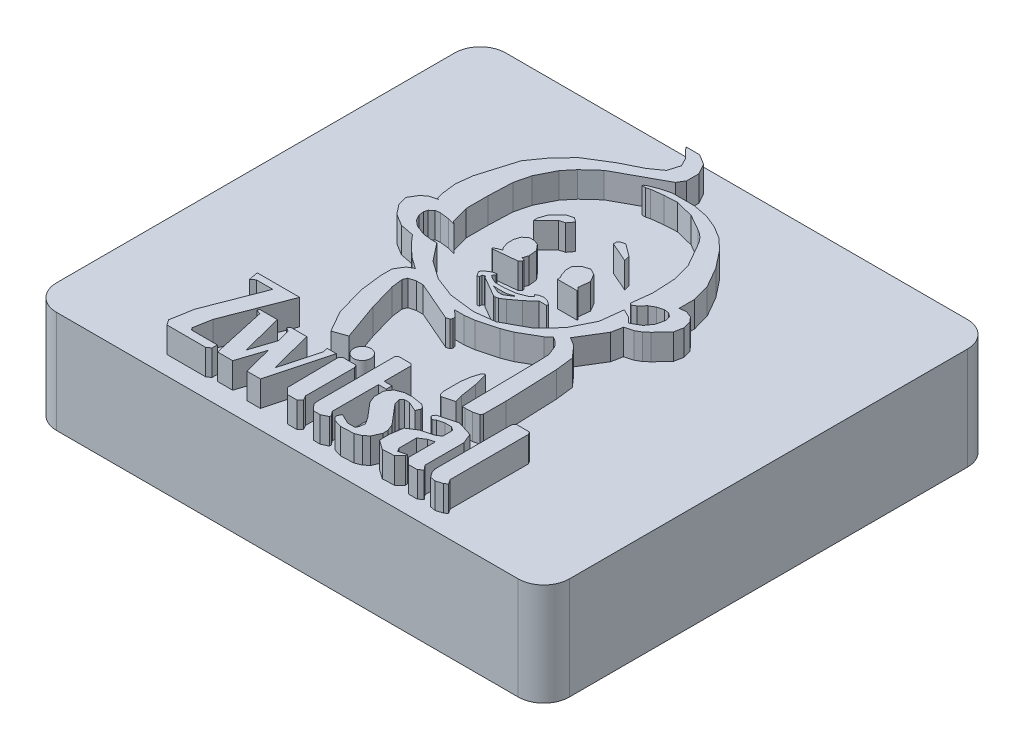
SolidWorks part; units mm, degrees
ref_plane "Front Plane" through (0, 0, 0) normal (0, 0, 1) x (1, 0, 0)
ref_plane "Top Plane" through (0, 0, 0) normal (0, 1, 0) x (1, 0, 0)
ref_plane "Right Plane" through (0, 0, 0) normal (1, 0, 0) x (0, 0, -1)
sketch "Sketch1" plane through (0, 0, 0) normal (0, 1, 0) x (1, 0, 0)
  line L1 (-100.2137, -87.7872) -> (100.2137, -87.7872)
  line L2 (-100.2137, -87.7872) -> (-100.2137, 87.7872)
  line L3 (-100.2137, 87.7872) -> (100.2137, 87.7872)
  line L4 (100.2137, -87.7872) -> (100.2137, 87.7872)
  line L5 (-100.2137, -87.7872) -> (100.2137, 87.7872) construction
  line L6 (-100.2137, 87.7872) -> (100.2137, -87.7872) construction
  point P0 (0, 0)
extrude "Boss-Extrude1" add sketch "Sketch1" along normal blind 40
fillet "Fillet1" radius 10 1 edges at (-100.2137, 20, -87.7872)
fillet "Fillet2" radius 10 1 edges at (100.2137, 20, -87.7872)
fillet "Fillet3" radius 10 1 edges at (100.2137, 20, 87.7872)
fillet "Fillet4" radius 10 1 edges at (-100.2137, 20, 87.7872)
sketch "Sketch2" plane through (0, 40, 0) normal (0, 1, 0) x (1, 0, 0)
  line L0 (306.3054, 1187.5992) -> (1789.6387, 1187.5992) construction
  line L1 (-54.3505, -45.1953) -> (-37.775, -45.1953)
  line L2 (-37.775, -45.1953) -> (-47.2756, -69.6543)
  line L3 (-47.2756, -69.6543) -> (-48.4884, -76.5271)
  line L4 (-48.4884, -76.5271) -> (-47.882, -77.3934)
  line L5 (-47.882, -77.3934) -> (-40.706, -77.3934)
  line L6 (-40.706, -77.3934) -> (-37.775, -77.3934)
  line L7 (-37.775, -77.3934) -> (-37.775, -79.4581)
  line L8 (-37.775, -79.4581) -> (-39.2405, -80.484)
  line L9 (-39.2405, -80.484) -> (-54.3505, -80.484)
  line L10 (-54.3505, -80.484) -> (-55.7913, -78.4258)
  line L11 (-55.7913, -78.4258) -> (-54.2433, -69.6543)
  line L12 (-54.2433, -69.6543) -> (-45.7365, -47.7536)
  line L13 (-45.7365, -47.7536) -> (-52.127, -47.7536)
  line L14 (-52.127, -47.7536) -> (-53.6655, -48.8306)
  line L15 (-53.6655, -48.8306) -> (-54.3505, -45.1953)
  line L16 (-41.5367, -57.1064) -> (-34.5884, -57.1064)
  line L17 (-34.5884, -57.1064) -> (-30.3919, -73.5484)
  line L18 (-30.3919, -73.5484) -> (-27.2443, -63.9885)
  line L19 (-27.2443, -63.9885) -> (-28.5356, -58.929)
  line L20 (-28.5356, -58.929) -> (-29.9995, -58.0604)
  line L21 (-29.9995, -58.0604) -> (-29.4334, -57.1064)
  line L22 (-29.4334, -57.1064) -> (-23.0997, -57.1064)
  line L23 (-23.0997, -57.1064) -> (-18.7793, -74.0335)
  line L24 (-18.7793, -74.0335) -> (-14.7067, -58.929)
  line L25 (-14.7067, -58.929) -> (-15.0501, -57.5834)
  line L26 (-15.0501, -57.5834) -> (-15.0501, -57.1064)
  line L27 (-15.0501, -57.1064) -> (-11.5421, -57.1064)
  line L28 (-11.5421, -57.1064) -> (-17.8455, -80.484)
  line L29 (-17.8455, -80.484) -> (-23.0997, -80.484)
  line L30 (-23.0997, -80.484) -> (-25.9729, -69.2263)
  line L31 (-25.9729, -69.2263) -> (-29.4334, -79.7361)
  line L32 (-29.4334, -79.7361) -> (-35.3452, -79.7361)
  line L33 (-35.3452, -79.7361) -> (-40.028, -58.4947)
  line L34 (-40.028, -58.4947) -> (-41.8031, -57.9103)
  line L35 (-41.8031, -57.9103) -> (-41.5367, -57.1064)
  line L36 (-9.0614, -57.1064) -> (-3.85, -57.1064)
  line L37 (-3.85, -57.1064) -> (-3.2808, -58.1815)
  line L38 (-3.2808, -58.1815) -> (-3.2808, -77.3934)
  line L39 (-3.2808, -77.3934) -> (-2.2898, -79.2654)
  line L40 (-2.2898, -79.2654) -> (-3.5654, -80.484)
  line L41 (-3.5654, -80.484) -> (-7.3461, -80.484)
  line L42 (-7.3461, -80.484) -> (-9.6446, -78.0779)
  line L43 (-9.6446, -78.0779) -> (-9.8746, -58.1815)
  line L44 (-9.8746, -58.1815) -> (-9.0614, -57.1064)
  line L45 (1.5966, -45.8731) -> (6.4741, -45.8731)
  line L46 (6.4741, -45.8731) -> (7.1619, -46.5609)
  line L47 (7.1619, -46.5609) -> (7.1619, -57.1064)
  line L48 (7.1619, -57.1064) -> (10.226, -57.1064)
  line L49 (10.226, -57.1064) -> (10.226, -59.3383)
  line L50 (10.226, -59.3383) -> (7.1619, -59.3383)
  line L51 (7.1619, -59.3383) -> (7.1619, -77.3934)
  line L52 (7.1619, -77.3934) -> (8.4015, -79.013)
  line L53 (8.4015, -79.013) -> (8.4015, -79.7361)
  line L54 (8.4015, -79.7361) -> (5.95, -80.8893)
  line L55 (5.95, -80.8893) -> (3.2634, -80.8893)
  line L56 (3.2634, -80.8893) -> (1.0295, -78.4258)
  line L57 (1.0295, -78.4258) -> (0.8619, -76.2764)
  line L58 (0.8619, -76.2764) -> (0.8619, -46.5609)
  line L59 (0.8619, -46.5609) -> (1.5966, -45.8731)
  line L60 (23.7545, -59.3383) -> (23.0196, -60.9979)
  line L61 (23.0196, -60.9979) -> (20.527, -59.8941)
  line L62 (20.527, -59.8941) -> (19.2719, -59.3383)
  line L63 (19.2719, -59.3383) -> (17.3668, -59.3383)
  line L64 (17.3668, -59.3383) -> (16.2592, -60.446)
  line L65 (16.2592, -60.446) -> (16.813, -62.5241)
  line L66 (16.813, -62.5241) -> (23.3871, -70.2685)
  line L67 (23.3871, -70.2685) -> (24.4894, -72.9818)
  line L68 (24.4894, -72.9818) -> (24.4894, -74.9038)
  line L69 (24.4894, -74.9038) -> (23.611, -76.8874)
  line L70 (23.611, -76.8874) -> (23.0196, -78.2229)
  line L71 (23.0196, -78.2229) -> (21.237, -79.7361)
  line L72 (21.237, -79.7361) -> (18.9465, -80.6667)
  line L73 (18.9465, -80.6667) -> (13.7794, -80.8893)
  line L74 (13.7794, -80.8893) -> (10.8865, -79.97)
  line L75 (10.8865, -79.97) -> (9.6031, -78.6866)
  line L76 (9.6031, -78.6866) -> (9.6031, -77.8905)
  line L77 (9.6031, -77.8905) -> (10.2448, -76.5271)
  line L78 (10.2448, -76.5271) -> (11.6931, -77.2088)
  line L79 (11.6931, -77.2088) -> (14.1715, -78.3753)
  line L80 (14.1715, -78.3753) -> (17.0524, -78.3753)
  line L81 (17.0524, -78.3753) -> (17.6014, -77.2088)
  line L82 (17.6014, -77.2088) -> (17.9127, -75.1628)
  line L83 (17.9127, -75.1628) -> (16.3629, -72.7591)
  line L84 (16.3629, -72.7591) -> (11.5018, -67.0327)
  line L85 (11.5018, -67.0327) -> (10.368, -64.2417)
  line L86 (10.368, -64.2417) -> (10.368, -60.446)
  line L87 (10.368, -60.446) -> (11.9809, -58.1815)
  line L88 (11.9809, -58.1815) -> (14.9883, -56.9598)
  line L89 (14.9883, -56.9598) -> (17.9127, -56.8337)
  line L90 (17.9127, -56.8337) -> (22.1283, -57.4752)
  line L91 (22.1283, -57.4752) -> (23.3871, -58.3718)
  line L92 (23.3871, -58.3718) -> (23.7545, -59.3383)
  line L93 (28.8189, -58.3718) -> (35.9344, -56.4755)
  line L94 (35.9344, -56.4755) -> (41.9018, -58.3718)
  line L95 (41.9018, -58.3718) -> (43.5155, -62.3438)
  line L96 (43.5155, -62.3438) -> (43.5155, -77.5551)
  line L97 (43.5155, -77.5551) -> (44.9812, -79.2817)
  line L98 (44.9812, -79.2817) -> (43.5155, -80.5259)
  line L99 (43.5155, -80.5259) -> (40.0158, -80.5259)
  line L100 (40.0158, -80.5259) -> (37.6572, -78.1672)
  line L101 (37.6572, -78.1672) -> (37.6572, -72.9818)
  line L102 (37.6572, -72.9818) -> (37.6572, -67.6324)
  line L103 (37.6572, -67.6324) -> (35.267, -68.2694)
  line L104 (35.267, -68.2694) -> (32.6613, -69.9495)
  line L105 (32.6613, -69.9495) -> (32.6613, -76.8874)
  line L106 (32.6613, -76.8874) -> (33.4866, -78.1672)
  line L107 (33.4866, -78.1672) -> (35.267, -77.6927)
  line L108 (35.267, -77.6927) -> (36.4621, -77.3742)
  line L109 (36.4621, -77.3742) -> (36.4621, -78.1672)
  line L110 (36.4621, -78.1672) -> (34.3768, -80.2525)
  line L111 (34.3768, -80.2525) -> (29.8284, -80.5259)
  line L112 (29.8284, -80.5259) -> (26.1285, -77.8905)
  line L113 (26.1285, -77.8905) -> (26.1285, -73.9428)
  line L114 (26.1285, -73.9428) -> (26.8639, -69.1094)
  line L115 (26.8639, -69.1094) -> (30.5763, -66.7158)
  line L116 (30.5763, -66.7158) -> (35.267, -65.4657)
  line L117 (35.267, -65.4657) -> (37.1653, -64.2417)
  line L118 (37.1653, -64.2417) -> (37.1653, -60.3578)
  line L119 (37.1653, -60.3578) -> (35.734, -59.3383)
  line L120 (35.734, -59.3383) -> (33.074, -59.3383)
  line L121 (33.074, -59.3383) -> (30.5763, -60.0039)
  line L122 (30.5763, -60.0039) -> (29.4478, -60.7316)
  line L123 (29.4478, -60.7316) -> (27.9785, -59.685)
  line L124 (27.9785, -59.685) -> (28.8189, -58.3718)
  line L125 (47.6216, -45.8731) -> (52.7453, -45.8731)
  line L126 (52.7453, -45.8731) -> (53.3033, -46.9209)
  line L127 (53.3033, -46.9209) -> (53.3033, -77.5551)
  line L128 (53.3033, -77.5551) -> (54.5152, -79.2817)
  line L129 (54.5152, -79.2817) -> (53.3033, -80.1323)
  line L130 (53.3033, -80.1323) -> (50.8305, -80.8893)
  line L131 (50.8305, -80.8893) -> (48.7016, -80.5108)
  line L132 (48.7016, -80.5108) -> (47.233, -78.4184)
  line L133 (47.233, -78.4184) -> (46.7643, -76.8874)
  line L134 (46.7643, -76.8874) -> (46.7643, -46.9209)
  line L135 (46.7643, -46.9209) -> (47.6216, -45.8731)
  line L136 (-13.1432, 81.2221) -> (-7.9144, 81.2221)
  line L137 (-7.9144, 81.2221) -> (-3.8492, 78.7248)
  line L138 (-3.8492, 78.7248) -> (-1.5929, 74.5885)
  line L139 (-1.5929, 74.5885) -> (-1.5929, 69.8279)
  line L140 (-1.5929, 69.8279) -> (-3.28, 67.0817)
  line L141 (-3.28, 67.0817) -> (-8.442, 64.2658)
  line L142 (-8.442, 64.2658) -> (-21.2696, 57.2684)
  line L143 (-21.2696, 57.2684) -> (-26.6675, 52.3283)
  line L144 (-26.6675, 52.3283) -> (-29.9986, 48.3481)
  line L145 (-29.9986, 48.3481) -> (-33.4907, 41.3937)
  line L146 (-33.4907, 41.3937) -> (-34.9864, 35.4394)
  line L147 (-34.9864, 35.4394) -> (-35.3444, 25.9167)
  line L148 (-35.3444, 25.9167) -> (-35.3444, 17.4167)
  line L149 (-35.3444, 17.4167) -> (-33.4907, 10.6168)
  line L150 (-33.4907, 10.6168) -> (-32.4808, 9.7716)
  line L151 (-32.4808, 9.7716) -> (-35.3444, 10.491)
  line L152 (-35.3444, 10.491) -> (-38.9083, 10.9209)
  line L153 (-38.9083, 10.9209) -> (-40.7052, 10.7059)
  line L154 (-40.7052, 10.7059) -> (-42.165, 9.3699)
  line L155 (-42.165, 9.3699) -> (-42.5251, 7.9364)
  line L156 (-42.5251, 7.9364) -> (-42.2834, 5.9158)
  line L157 (-42.2834, 5.9158) -> (-41.1194, 3.7819)
  line L158 (-41.1194, 3.7819) -> (-38.9083, 1.9314)
  line L159 (-38.9083, 1.9314) -> (-34.9864, 0.4291)
  line L160 (-34.9864, 0.4291) -> (-31.7446, 0.0381)
  line L161 (-31.7446, 0.0381) -> (-29.4326, 0.0381)
  line L162 (-29.4326, 0.0381) -> (-23.9686, -6.8987)
  line L163 (-23.9686, -6.8987) -> (-17.0316, -11.8156)
  line L164 (-17.0316, -11.8156) -> (-9.0606, -14.8688)
  line L165 (-9.0606, -14.8688) -> (-5.0221, -15.356)
  line L166 (-5.0221, -15.356) -> (0.8627, -16.0658)
  line L167 (0.8627, -16.0658) -> (8.8331, -15.1124)
  line L168 (8.8331, -15.1124) -> (18.4848, -9.8474)
  line L169 (18.4848, -9.8474) -> (24.4902, -3.4303)
  line L170 (24.4902, -3.4303) -> (28.8197, 5.1921)
  line L171 (28.8197, 5.1921) -> (29.6782, 12.3093)
  line L172 (29.6782, 12.3093) -> (29.8842, 14.0168)
  line L173 (29.8842, 14.0168) -> (31.1085, 13.402)
  line L174 (31.1085, 13.402) -> (33.0748, 12.4147)
  line L175 (33.0748, 12.4147) -> (34.671, 10.9209)
  line L176 (34.671, 10.9209) -> (35.2678, 10.3623)
  line L177 (35.2678, 10.3623) -> (38.8538, 12.4147)
  line L178 (38.8538, 12.4147) -> (40.7565, 15.0992)
  line L179 (40.7565, 15.0992) -> (41.62, 18.5366)
  line L180 (41.62, 18.5366) -> (41.0725, 20.545)
  line L181 (41.0725, 20.545) -> (39.49, 21.6667)
  line L182 (39.49, 21.6667) -> (37.658, 21.8877)
  line L183 (37.658, 21.8877) -> (35.2678, 21.2361)
  line L184 (35.2678, 21.2361) -> (33.0748, 19.9809)
  line L185 (33.0748, 19.9809) -> (31.0196, 17.7849)
  line L186 (31.0196, 17.7849) -> (29.5478, 16.9425)
  line L187 (29.5478, 16.9425) -> (28.8197, 17.4586)
  line L188 (28.8197, 17.4586) -> (29.755, 25.2122)
  line L189 (29.755, 25.2122) -> (29.2874, 34.5514)
  line L190 (29.2874, 34.5514) -> (27.4221, 41.3937)
  line L191 (27.4221, 41.3937) -> (22.1291, 50.6417)
  line L192 (17.3676, 55.3916) -> (11.0575, 58.9828)
  line L193 (11.0575, 58.9828) -> (3.9528, 60.7676)
  line L194 (3.9528, 60.7676) -> (-1.031, 60.518)
  line L195 (-1.031, 60.518) -> (-5.8619, 59.9401)
  line L196 (-5.8619, 59.9401) -> (-7.3461, 59.5355)
  line L197 (-7.3461, 59.5355) -> (-8.6735, 59.5355)
  line L198 (-8.6735, 59.5355) -> (-8.5719, 59.9401)
  line L199 (-8.5719, 59.9401) -> (-7.3461, 60.6417)
  line L200 (-7.3461, 60.6417) -> (-4.4076, 61.7795)
  line L201 (-4.4076, 61.7795) -> (-0.2695, 62.9076)
  line L202 (-0.2695, 62.9076) -> (3.8457, 62.9076)
  line L203 (3.8457, 62.9076) -> (8.4015, 62.9076)
  line L204 (8.4015, 62.9076) -> (14.2122, 61.7795)
  line L205 (14.2122, 61.7795) -> (19.2719, 59.7378)
  line L206 (19.2719, 59.7378) -> (24.047, 56.8043)
  line L207 (24.047, 56.8043) -> (28.232, 52.8878)
  line L208 (28.232, 52.8878) -> (33.6807, 45.9705)
  line L209 (33.6807, 45.9705) -> (38.258, 37.973)
  line L210 (38.258, 37.973) -> (40.0832, 31.2775)
  line L211 (40.0832, 31.2775) -> (40.0832, 25.2126)
  line L212 (40.0832, 25.2126) -> (42.7254, 25.5287)
  line L213 (42.7254, 25.5287) -> (45.2017, 24.5295)
  line L214 (45.2017, 24.5295) -> (46.7643, 22.7357)
  line L215 (46.7643, 22.7357) -> (47.6216, 19.5908)
  line L216 (47.6216, 19.5908) -> (46.9531, 16.1475)
  line L217 (46.9531, 16.1475) -> (44.7159, 13.7569)
  line L218 (44.7159, 13.7569) -> (42.7254, 11.63)
  line L219 (42.7254, 11.63) -> (40.8901, 10.0312)
  line L220 (40.8901, 10.0312) -> (38.8538, 8.8658)
  line L221 (38.8538, 8.8658) -> (35.6149, 7.9828)
  line L222 (35.6149, 7.9828) -> (34.7993, 3.7819)
  line L223 (34.7993, 3.7819) -> (32.476, 0)
  line L224 (32.476, 0) -> (29.9483, -4.1144)
  line L225 (29.9483, -4.1144) -> (28.8197, -5.9515)
  line L226 (28.8197, -5.9515) -> (32.0916, -7.9615)
  line L227 (32.0916, -7.9615) -> (36.0275, -12.4799)
  line L228 (36.0275, -12.4799) -> (36.8599, -19.4386)
  line L229 (36.8599, -19.4386) -> (37.6572, -39.9253)
  line L230 (37.6572, -39.9253) -> (37.6572, -48.8306)
  line L231 (37.6572, -48.8306) -> (37.1653, -49.6311)
  line L232 (37.1653, -49.6311) -> (34.7993, -50.2761)
  line L233 (34.7993, -50.2761) -> (32.0916, -50.3815)
  line L234 (32.0916, -50.3815) -> (30.9564, -50.3815)
  line L235 (30.9564, -50.3815) -> (30.9042, -49.0402)
  line L236 (30.9042, -49.0402) -> (30.4557, -20.2047)
  line L237 (30.4557, -20.2047) -> (30.2905, -15.9593)
  line L238 (30.2905, -15.9593) -> (28.8197, -12.1611)
  line L239 (28.8197, -12.1611) -> (27.1295, -10.2207)
  line L240 (27.1295, -10.2207) -> (25.3141, -9.1055)
  line L241 (25.3141, -9.1055) -> (23.3871, -10.7841)
  line L242 (23.3871, -10.7841) -> (20.0406, -12.6995)
  line L243 (20.0406, -12.6995) -> (15.8247, -15.1124)
  line L244 (15.8247, -15.1124) -> (11.9809, -16.6008)
  line L245 (11.9809, -16.6008) -> (7.8652, -17.7227)
  line L246 (7.8652, -17.7227) -> (4.2854, -18.6986)
  line L247 (4.2854, -18.6986) -> (0.4904, -19.1526)
  line L248 (0.4904, -19.1526) -> (-3.2808, -19.1526)
  line L249 (-3.2808, -19.1526) -> (-2.0797, -20.2767)
  line L250 (-2.0797, -20.2767) -> (-0.8546, -21.4231)
  line L251 (-0.8546, -21.4231) -> (-0.5877, -22.4022)
  line L252 (-0.5877, -22.4022) -> (-1.0954, -23.2285)
  line L253 (-1.0954, -23.2285) -> (-2.3579, -23.5727)
  line L254 (-2.3579, -23.5727) -> (-14.7067, -18.2107)
  line L255 (-14.7067, -18.2107) -> (-17.8455, -16.8477)
  line L256 (-17.8455, -16.8477) -> (-20.5001, -16.8477)
  line L257 (-20.5001, -16.8477) -> (-23.0997, -17.5564)
  line L258 (-23.0997, -17.5564) -> (-23.7927, -19.1526)
  line L259 (-23.7927, -19.1526) -> (-23.264, -23.5727)
  line L260 (-23.264, -23.5727) -> (-20.2499, -34.0623)
  line L261 (-20.2499, -34.0623) -> (-15.0501, -48.6693)
  line L262 (-15.0501, -48.6693) -> (-20.2499, -50.5203)
  line L263 (-20.2499, -50.5203) -> (-24.9503, -42.3077)
  line L264 (-24.9503, -42.3077) -> (-28.2875, -30.694)
  line L265 (-28.2875, -30.694) -> (-29.3379, -21.9127)
  line L266 (-29.3379, -21.9127) -> (-29.3379, -17.5564)
  line L267 (-29.3379, -17.5564) -> (-27.2443, -14.1484)
  line L268 (-27.2443, -14.1484) -> (-24.9503, -12.8355)
  line L269 (-24.9503, -12.8355) -> (-29.3379, -9.7256)
  line L270 (-29.3379, -9.7256) -> (-33.9126, -5.4444)
  line L271 (-33.9126, -5.4444) -> (-36.9474, -1.9606)
  line L272 (-36.9474, -1.9606) -> (-42.2834, -0.9246)
  line L273 (-42.2834, -0.9246) -> (-46.9323, 1.9314)
  line L274 (-46.9323, 1.9314) -> (-49.8417, 5.625)
  line L275 (-49.8417, 5.625) -> (-50.8626, 9.3699)
  line L276 (-50.8626, 9.3699) -> (-48.8079, 12.7145)
  line L277 (-48.8079, 12.7145) -> (-46.9323, 14.1919)
  line L278 (-46.9323, 14.1919) -> (-43.6041, 15.0992)
  line L279 (-43.6041, 15.0992) -> (-44.3738, 15.2486)
  line L280 (-44.3738, 15.2486) -> (-45.0652, 17.7849)
  line L281 (-45.0652, 17.7849) -> (-45.7647, 23.6326)
  line L282 (-45.7647, 23.6326) -> (-45.0109, 29.8818)
  line L283 (-45.0109, 29.8818) -> (-40.7052, 44.3054)
  line L284 (-40.7052, 44.3054) -> (-36.4291, 50.3382)
  line L285 (-36.4291, 50.3382) -> (-30.5886, 56.5791)
  line L286 (-30.5886, 56.5791) -> (-21.2696, 62.3436)
  line L287 (-21.2696, 62.3436) -> (-13.7226, 66.0996)
  line L288 (-13.7226, 66.0996) -> (-9.0606, 69.4328)
  line L289 (-9.0606, 69.4328) -> (-7.7178, 73.9309)
  line L290 (-7.7178, 73.9309) -> (-9.3636, 77.2377)
  line L291 (-9.3636, 77.2377) -> (-11.8031, 79.5207)
  line L292 (-11.8031, 79.5207) -> (-13.1432, 81.2221)
  line L293 (23.3871, -51.1888) -> (27.9785, -49.9319)
  line L294 (27.9785, -49.9319) -> (27.1295, -46.8307)
  line L295 (27.1295, -46.8307) -> (26.1285, -40.409)
  line L296 (26.1285, -40.409) -> (24.9285, -36.0255)
  line L297 (24.9285, -36.0255) -> (24.6665, -35.0683)
  line L298 (24.6665, -35.0683) -> (24.221, -35.0683)
  line L299 (24.221, -35.0683) -> (23.611, -35.6783)
  line L300 (23.611, -35.6783) -> (22.6673, -38.5596)
  line L301 (22.6673, -38.5596) -> (22.1283, -42.3077)
  line L302 (22.1283, -42.3077) -> (22.1283, -46.5609)
  line L303 (22.1283, -46.5609) -> (22.1283, -49.0402)
  line L304 (22.1283, -49.0402) -> (22.5444, -50.5603)
  line L305 (22.5444, -50.5603) -> (23.3871, -51.1888)
  line L306 (-11.019, 35.4394) -> (-13.7226, 34.6994)
  line L307 (-13.7226, 34.6994) -> (-17.0316, 31.3903)
  line L308 (-17.0316, 31.3903) -> (-18.1221, 28.0609)
  line L309 (-18.1221, 28.0609) -> (-18.1221, 26.4302)
  line L310 (-18.1221, 26.4302) -> (-15.3771, 29.1753)
  line L311 (-15.3771, 29.1753) -> (-13.1432, 31.4092)
  line L312 (-13.1432, 31.4092) -> (-11.019, 31.9906)
  line L313 (-11.019, 31.9906) -> (-9.3636, 34.2104)
  line L314 (-9.3636, 34.2104) -> (-11.019, 35.4394)
  line L315 (5.4321, 34.2104) -> (13.235, 30.7868)
  line L316 (13.235, 30.7868) -> (12.6017, 33.1005)
  line L317 (12.6017, 33.1005) -> (10.226, 34.8644)
  line L318 (10.226, 34.8644) -> (7.8652, 36.6172)
  line L319 (7.8652, 36.6172) -> (5.95, 36.0929)
  line L320 (5.95, 36.0929) -> (5.4321, 35.3955)
  line L321 (5.4321, 35.3955) -> (5.4321, 34.2104)
  line L322 (-16.4181, 8.8658) -> (-7.3461, 9.7716)
  line L323 (-7.3461, 9.7716) -> (-6.5625, 10.7291)
  line L324 (-6.5625, 10.7291) -> (-6.6176, 11.281)
  line L325 (-6.6176, 11.281) -> (-7.7178, 11.63)
  line L326 (-7.7178, 11.63) -> (-7.0432, 13.7569)
  line L327 (-7.0432, 13.7569) -> (-7.3613, 16.9425)
  line L328 (-7.3613, 16.9425) -> (-9.3636, 19.2824)
  line L329 (-9.3636, 19.2824) -> (-11.2844, 19.8916)
  line L330 (-11.2844, 19.8916) -> (-13.1432, 19.8916)
  line L331 (-13.1432, 19.8916) -> (-14.861, 18.4217)
  line L332 (-14.861, 18.4217) -> (-15.5823, 16.1475)
  line L333 (-15.5823, 16.1475) -> (-15.5823, 13.7569)
  line L334 (-15.5823, 13.7569) -> (-14.861, 11.4555)
  line L335 (-14.861, 11.4555) -> (-14.0021, 10.4517)
  line L336 (-14.0021, 10.4517) -> (-15.8923, 9.8593)
  line L337 (-15.8923, 9.8593) -> (-16.8264, 9.06)
  line L338 (-16.8264, 9.06) -> (-16.4181, 8.8658)
  line L339 (6.4741, 11.281) -> (14.2122, 11.281)
  line L340 (14.2122, 11.281) -> (14.2122, 11.63)
  line L341 (14.2122, 11.63) -> (13.235, 12.6071)
  line L342 (13.235, 12.6071) -> (13.7236, 16.9425)
  line L343 (13.7236, 16.9425) -> (11.9809, 19.9809)
  line L344 (11.9809, 19.9809) -> (9.6031, 21.2361)
  line L345 (9.6031, 21.2361) -> (6.9002, 20.4009)
  line L346 (6.9002, 20.4009) -> (4.961, 18.4617)
  line L347 (4.961, 18.4617) -> (4.961, 16.1475)
  line L348 (4.961, 16.1475) -> (5.6997, 13.7569)
  line L349 (5.6997, 13.7569) -> (6.4741, 12.4068)
  line L350 (6.4741, 12.4068) -> (6.4741, 11.281)
  line L351 (-7.7178, -0.2665) -> (-7.0432, 0.7197)
  line L352 (-7.0432, 0.7197) -> (-7.1595, 1.3394)
  line L353 (-7.1595, 1.3394) -> (-8.6735, 1.0296)
  line L354 (-8.6735, 1.0296) -> (-10.2948, 0)
  line L355 (-10.2948, 0) -> (-11.2844, -0.9246)
  line L356 (-11.2844, -0.9246) -> (-11.5421, -1.5235)
  line L357 (-11.5421, -1.5235) -> (-10.5329, -3.1127)
  line L358 (-10.5329, -3.1127) -> (-9.6446, -3.1127)
  line L359 (-9.6446, -3.1127) -> (-9.6446, -2.074)
  line L360 (-9.6446, -2.074) -> (-9.0606, -1.7031)
  line L361 (-9.0606, -1.7031) -> (-8.442, -1.8412)
  line L362 (-8.442, -1.8412) -> (-8.442, -2.1477)
  line L363 (-8.442, -2.1477) -> (-0.5877, -6.6769)
  line L364 (-0.5877, -6.6769) -> (0.2786, -6.8703)
  line L365 (0.2786, -6.8703) -> (1.3726, -6.6464)
  line L366 (1.3726, -6.6464) -> (3.2634, -5.4457)
  line L367 (3.2634, -5.4457) -> (6.9002, -2.7859)
  line L368 (6.9002, -2.7859) -> (9.6031, -0.2605)
  line L369 (9.6031, -0.2605) -> (10.226, 0.3215)
  line L370 (10.226, 0.3215) -> (13.235, 0.3215)
  line L371 (13.235, 0.3215) -> (13.235, 1.0296)
  line L372 (13.235, 1.0296) -> (11.5018, 2.2151)
  line L373 (11.5018, 2.2151) -> (9.9145, 2.5695)
  line L374 (9.9145, 2.5695) -> (8.4015, 2.2598)
  line L375 (8.4015, 2.2598) -> (7.1619, 1.6223)
  line L376 (7.1619, 1.6223) -> (7.7817, 0.959)
  line L377 (7.7817, 0.959) -> (7.7184, 0.6756)
  line L378 (7.7184, 0.6756) -> (6.4385, -0.2605)
  line L379 (6.4385, -0.2605) -> (3.0776, -1.5232)
  line L380 (3.0776, -1.5232) -> (-1.0954, -1.9945)
  line L381 (-1.0954, -1.9945) -> (-4.5149, -1.9945)
  line L382 (-4.5149, -1.9945) -> (-6.6176, -1.0897)
  line L383 (-6.6176, -1.0897) -> (-7.7178, -0.2665)
  line L384 (-3.85, -3.4303) -> (-0.8546, -4.7205)
  line L385 (-0.8546, -4.7205) -> (0.8627, -4.7205)
  line L386 (0.8627, -4.7205) -> (4.0648, -2.7859)
  line L387 (3.7069, -2.6976) -> (1.5966, -3.4303)
  line L388 (1.5966, -3.4303) -> (-0.2695, -3.5805)
  line L389 (-0.2695, -3.5805) -> (-2.0797, -3.5805)
  line L390 (-2.0797, -3.5805) -> (-3.85, -3.4303)
  circle A0 centre (-6.5625, -51.983) radius 3.3835
  arc A1 (22.1291, 50.6417) -> (17.3676, 55.3916) centre (11.0583, 44.3054) ccw
  arc A2 (4.0648, -2.7859) -> (3.7069, -2.6976) centre (3.93, -2.5628) cw
extrude "Boss-Extrude2" add sketch "Sketch2" along normal blind 10
